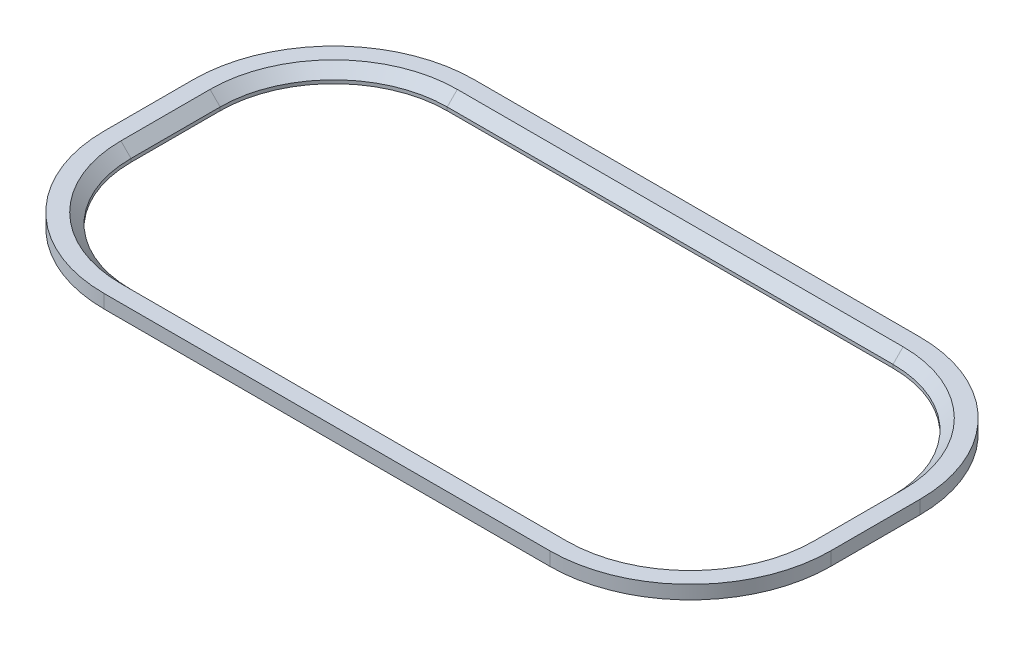
SolidWorks part; units mm, degrees
ref_plane "Front Plane" through (0, 0, 0) normal (0, 0, 1) x (1, 0, 0)
ref_plane "Top Plane" through (0, 0, 0) normal (0, 1, 0) x (1, 0, 0)
ref_plane "Right Plane" through (0, 0, 0) normal (1, 0, 0) x (0, 0, -1)
sketch "Sketch1" plane through (0, 0, 0) normal (0, 1, 0) x (1, 0, 0)
  line L0 (0, 0) -> (83.82, 0)
  line L1 (105.1646, 21.3446) -> (105.1646, 38.1086)
  line L2 (83.82, 59.4532) -> (0, 59.4532)
  line L3 (-21.3446, 38.1086) -> (-21.3446, 21.3446)
  line L8 (0, -5.08) -> (83.82, -5.08)
  line L9 (110.2446, 21.3446) -> (110.2446, 38.1086)
  line L10 (83.82, 64.5332) -> (0, 64.5332)
  line L11 (-26.4246, 38.1086) -> (-26.4246, 21.3446)
  arc A0 (83.82, 0) -> (105.1646, 21.3446) centre (83.82, 21.3446) ccw
  arc A1 (105.1646, 38.1086) -> (83.82, 59.4532) centre (83.82, 38.1086) ccw
  arc A2 (0, 59.4532) -> (-21.3446, 38.1086) centre (0, 38.1086) ccw
  arc A3 (-21.3446, 21.3446) -> (0, 0) centre (0, 21.3446) ccw
  arc A8 (83.82, -5.08) -> (110.2446, 21.3446) centre (83.82, 21.3446) ccw
  arc A9 (110.2446, 38.1086) -> (83.82, 64.5332) centre (83.82, 38.1086) ccw
  arc A10 (0, 64.5332) -> (-26.4246, 38.1086) centre (0, 38.1086) ccw
  arc A11 (-26.4246, 21.3446) -> (0, -5.08) centre (0, 21.3446) ccw
  dimension "D3" = 33.528
  dimension "D4" = 33.528
  dimension "D1" = 83.82
  dimension "D2" = 16.764
  dimension "D5" = 83.82
  dimension "D6" = 33.528
  dimension "D7" = 5.08
extrude "Boss-Extrude1" add sketch "Sketch1" along normal blind 2.54
chamfer "Chamfer1" distance 1.905 angle 45 8 edges at (98.9129, 2.54, -6.2517) (105.1646, 2.54, -29.7266) (98.9129, 2.54, -53.2015) (41.91, 2.54, -59.4532) (-15.0929, 2.54, -53.2015) (-21.3446, 2.54, -29.7266) (-15.0929, 2.54, -6.2517) (41.91, 2.54, 0)
